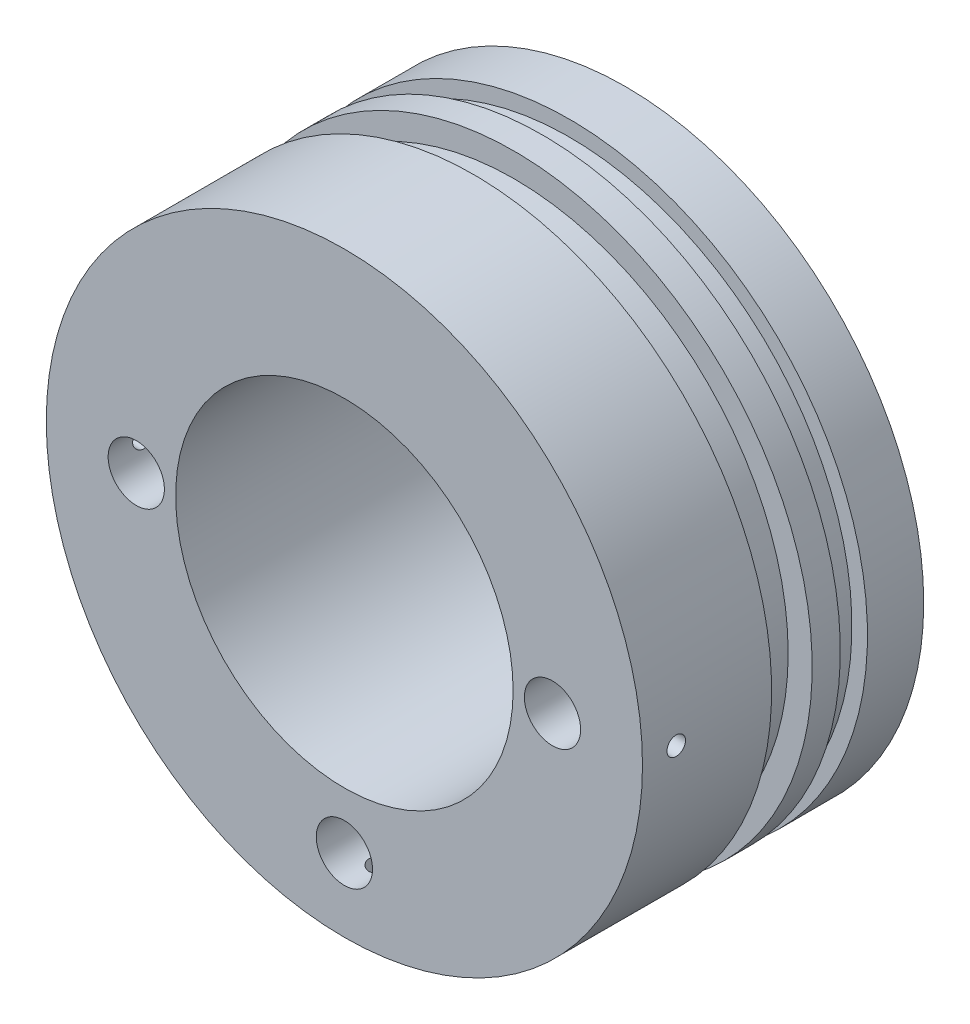
SolidWorks part; units mm, degrees
material "1060 Alloy"
ref_plane "Front Plane" through (0, 0, 0) normal (0, 0, 1) x (1, 0, 0)
ref_plane "Top Plane" through (0, 0, 0) normal (0, 1, 0) x (1, 0, 0)
ref_plane "Right Plane" through (0, 0, 0) normal (1, 0, 0) x (0, 0, -1)
sketch "Sketch1" plane through (0, 0, 0) normal (0, 0, 1) x (1, 0, 0)
  circle A0 centre (0, 0) radius 53
  dimension "D1" = 106
extrude "Boss-Extrude1" add sketch "Sketch1" along normal blind 50
hole_wizard "Ø10.0 (10) Diameter Hole2" positions "Sketch7" profile "Sketch9" hole size "Ø10.0" standard "ISO"
sketch "Sketch7" plane through (0, 0, 50) normal (0, 0, 1) x (1, 0, 0)
  point P0 (-37, 0)
  point P2 (37, 0)
  point P4 (0, -40)
  dimension "D1" = 37
  dimension "D2" = 37
  dimension "D3" = 40
sketch "Sketch9" plane through (-37, 0, 50) normal (1, 0, 0) x (0, -1, 0)
  line L0 (0, 0) -> (0, 20.5043)
  line L1 (0, 20.5043) -> (5, 17.5)
  line L2 (5, 17.5) -> (5, 0)
  line L5 (5, 0) -> (0, 0)
  line L10 (0, 20.5043) -> (-5, 17.5) construction
  line L11 (0, -6.35) -> (0, 107.95) construction
  dimension "Hole Dia." = 10
  dimension "Hole Depth" = 17.5
  dimension "Drill Angle" = 118
ref_plane "Plane1" through (-53, 0, 0) normal (-1, 0, 0) x (0, 0, 1)
hole_wizard "M4 Tapped Hole1" positions "Sketch4" profile "Sketch5" tap size "M4" standard "ISO"
sketch "Sketch4" plane through (-53, 0, 0) normal (-1, 0, 0) x (0, 0, 1)
  line L0 (50, -53) -> (50, 53) construction
  point P0 (44, 0)
  dimension "D1" = 6
sketch "Sketch5" plane through (-53, 0, 44) normal (0, 1, 0) x (0, 0, 1)
  line L0 (0, 0) -> (0, 85)
  line L1 (0, 85) -> (1.65, 85)
  line L2 (1.65, 85) -> (1.65, 0)
  line L5 (1.65, 0) -> (0, 0)
  line L11 (0, -6.35) -> (0, 107.95) construction
  dimension "Thru Tap Drill Dia." = 3.3
  dimension "Thru Tap Drill Depth" = 85
cosmetic thread "Hole Thread1" parameters "D2"=4
pattern_circular "CirPattern1" count 3 every 90 about axis through (0, 0, 50) along (0, 0, 1) of "M4 Tapped Hole1"
sketch "Sketch11" plane through (0, 0, 50) normal (0, 0, 1) x (1, 0, 0)
  circle A0 centre (0, 0) radius 30
  dimension "D1" = 60
extrude "Cut-Extrude2" cut sketch "Sketch11" against normal blind 45
sketch "Sketch12" plane through (0, 0, 0) normal (1, 0, 0) x (0, 0, -1)
  line L0 (0, 53) -> (-50, 53) construction
  line L1 (-10, 53) -> (-14.826, 53)
  line L2 (-10, 53) -> (-10, 50.2348)
  line L3 (-10, 50.2348) -> (-14.826, 50.2348)
  line L4 (-14.826, 53) -> (-14.826, 50.2348)
  line L5 (0, -53) -> (0, 53) construction
  line L6 (0, 0) -> (-18.8162, 0) construction
  line L8 (-19.826, 53) -> (-27.0396, 53)
  line L9 (-19.826, 53) -> (-19.826, 48.7274)
  line L10 (-19.826, 48.7274) -> (-27.0396, 48.7274)
  line L11 (-27.0396, 53) -> (-27.0396, 48.7274)
  point P14 (-19.826, 50.8637)
  dimension "D1" = 10
  dimension "D2" = 4.826
  dimension "D3" = 50.2348
  dimension "D4" = 7.2136
  dimension "D5" = 5
  dimension "D6" = 48.7274
revolve "Cut-Revolve1" cut sketch "Sketch12" angle 360 about L6
sketch "Sketch14" plane through (0, 0, 0) normal (1, 0, 0) x (0, 0, -1)
  line L0 (0, -53) -> (0, 53) construction
  line L1 (0, 27.1526) -> (-2.667, 27.1526)
  line L2 (0, 27.1526) -> (0, 22.5806)
  line L3 (0, 22.5806) -> (-2.667, 22.5806)
  line L4 (-2.667, 27.1526) -> (-2.667, 22.5806)
  line L6 (0, 0) -> (21.0083, 0) construction
  dimension "D1" = 2.667
  dimension "D2" = 4.572
  dimension "D3" = 22.5806
revolve "Cut-Revolve2" cut sketch "Sketch14" angle 360 about L6
hole_wizard "M5 Tapped Hole1" positions "Sketch16" profile "Sketch17" tap size "M5" standard "ISO"
sketch "Sketch16" plane through (0, 0, 0) normal (0, 0, -1) x (-1, 0, 0)
  line L0 (0, 0) -> (28.2843, 28.2843) construction
  line L3 (0, 0) -> (0, 39.1182) construction
  point P0 (28.2843, 28.2843)
  dimension "D1" = 45
  dimension "D2" = 40
sketch "Sketch17" plane through (-28.2843, 28.2843, 0) normal (1, 0, 0) x (0, 1, 0)
  line L0 (0, 0) -> (0, 15.2618)
  line L1 (0, 15.2618) -> (2.1, 14)
  line L2 (2.1, 14) -> (2.1, 0)
  line L5 (2.1, 0) -> (0, 0)
  line L10 (0, 15.2618) -> (-2.1, 14) construction
  line L11 (0, -6.35) -> (0, 107.95) construction
  dimension "Tap Drill Dia." = 4.2
  dimension "Tap Drill Depth" = 14
  dimension "Drill Angle" = 118
pattern_circular "CirPattern2" count 4 over 360 about axis through (0, 0, 0) along (0, 0, 1) of "M5 Tapped Hole1"
equation "\"3.995هى\"=42.5"
